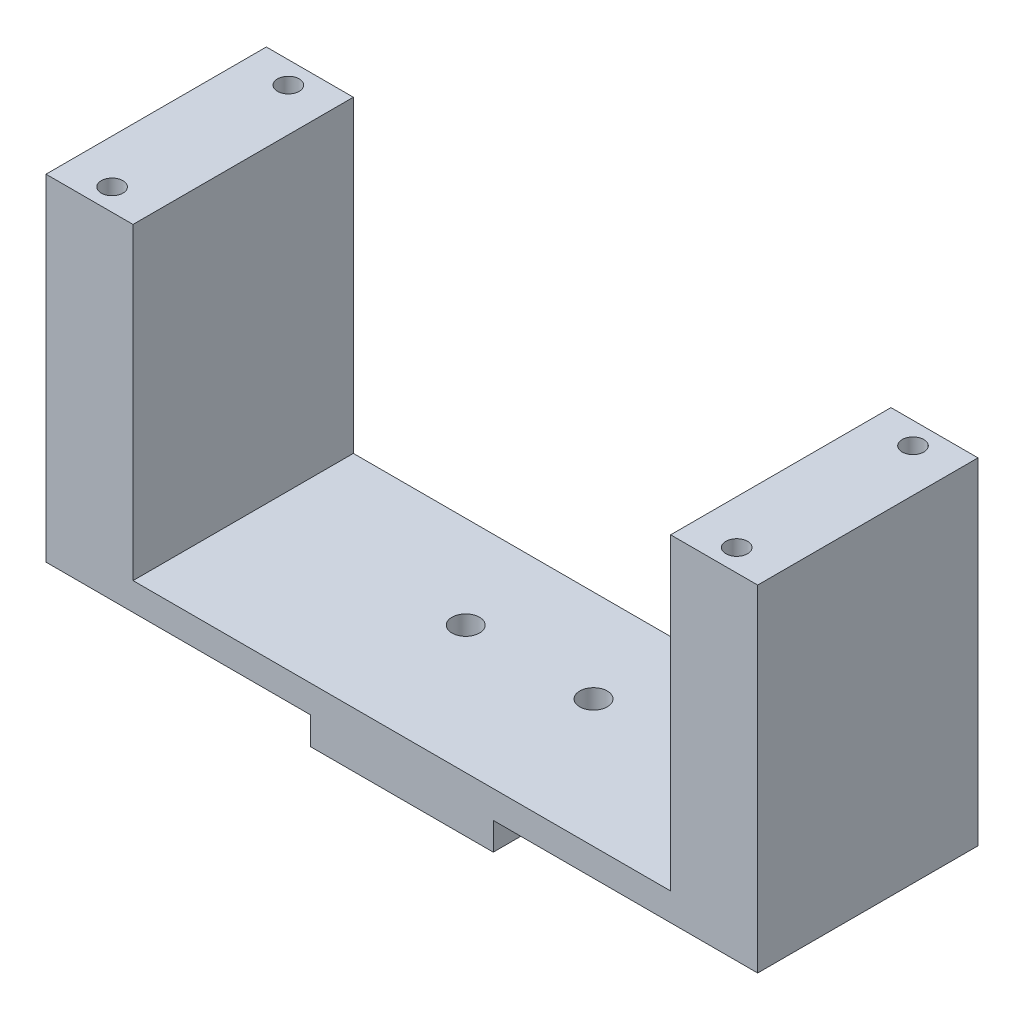
SolidWorks part; units mm, degrees
ref_plane "Front Plane" through (0, 0, 0) normal (0, 0, 1) x (1, 0, 0)
ref_plane "Top Plane" through (0, 0, 0) normal (0, 1, 0) x (1, 0, 0)
ref_plane "Right Plane" through (0, 0, 0) normal (1, 0, 0) x (0, 0, -1)
sketch "Sketch1" plane through (0, 0, 0) normal (0, 1, 0) x (1, 0, 0)
  line L1 (-31.1117, -8.3915) -> (38.7383, -8.3915)
  line L2 (-31.1117, -8.3915) -> (-31.1117, 17.0085)
  line L3 (-31.1117, 17.0085) -> (38.7383, 17.0085)
  line L4 (38.7383, -8.3915) -> (38.7383, 17.0085)
  dimension "D1" = 69.85
  dimension "D2" = 25.4
extrude "Boss-Extrude1" add sketch "Sketch1" along normal blind 3.175
sketch "Sketch2" plane through (0, 3.175, 0) normal (0, 1, 0) x (1, 0, 0)
  line L0 (-31.1117, -8.3915) -> (38.7383, -8.3915) construction
  line L1 (-31.1117, 17.0085) -> (-27.1747, 17.0085)
  line L2 (-31.1117, 17.0085) -> (-31.1117, -8.3915)
  line L3 (-31.1117, -8.3915) -> (-27.1747, -8.3915)
  line L4 (-27.1747, 17.0085) -> (-27.1747, -8.3915)
  line L5 (38.7383, 17.0085) -> (-31.1117, 17.0085) construction
  line L6 (38.7383, 17.0085) -> (34.8013, 17.0085)
  line L7 (38.7383, 17.0085) -> (38.7383, -8.3915)
  line L8 (38.7383, -8.3915) -> (34.8013, -8.3915)
  line L9 (34.8013, 17.0085) -> (34.8013, -8.3915)
  line L10 (38.7383, -8.3915) -> (38.7383, 17.0085) construction
  dimension "D1" = 3.937
  dimension "D2" = 3.937
  dimension "D3" = 0
extrude "Boss-Extrude2" add sketch "Sketch2" along normal blind 35.56 contours L4 L9 L2 L3
sketch "Sketch6" plane through (0, 0, 0) normal (0, -1, 0) x (1, 0, 0)
  line L0 (-31.1117, -17.0085) -> (-31.1117, 8.3915) construction
  line L1 (38.7383, 8.3915) -> (38.7383, -17.0085) construction
  line L2 (38.7383, -17.0085) -> (-31.1117, -17.0085) construction
  circle A0 centre (-3.5527, -6.3405) radius 1.5875
  circle A1 centre (11.1793, -6.3405) radius 1.5875
  dimension "D1" = 3.175
  dimension "D2" = 3.175
  dimension "D3" = 14.732
  dimension "D4" = 27.559
  dimension "D5" = 27.559
  dimension "D6" = 10.668
extrude "Cut-Extrude1" cut sketch "Sketch6" against normal blind 35.56
sketch "Sketch10" plane through (-31.1117, 0, 0) normal (-1, 0, 0) x (0, 0, 1)
  line L1 (-17.0085, 38.735) -> (8.3915, 38.735)
  line L2 (-17.0085, 38.735) -> (-17.0085, 0)
  line L3 (-17.0085, 0) -> (8.3915, 0)
  line L4 (8.3915, 38.735) -> (8.3915, 0)
extrude "Boss-Extrude3" add sketch "Sketch10" along normal blind 6.096
sketch "Sketch11" plane through (38.7383, 0, 0) normal (1, 0, 0) x (0, 0, -1)
  line L1 (17.0085, 38.735) -> (-8.3915, 38.735)
  line L2 (17.0085, 38.735) -> (17.0085, 0)
  line L3 (17.0085, 0) -> (-8.3915, 0)
  line L4 (-8.3915, 38.735) -> (-8.3915, 0)
extrude "Boss-Extrude4" add sketch "Sketch11" along normal blind 6.096
sketch "Sketch14" plane through (0, 38.735, 0) normal (0, 1, 0) x (1, 0, 0)
  line L0 (-37.2077, 17.0085) -> (-27.1747, 17.0085) construction
  line L1 (-37.2077, -8.3915) -> (-27.1747, -8.3915) construction
  line L2 (34.8013, -8.3915) -> (44.8343, -8.3915) construction
  line L3 (44.8343, 17.0085) -> (34.8013, 17.0085) construction
  line L4 (34.8013, 17.0085) -> (34.8013, -8.3915) construction
  line L5 (34.8013, 17.0085) -> (34.8013, -8.3915) construction
  line L6 (-37.2077, -8.3915) -> (-37.2077, 17.0085) construction
  circle A0 centre (-32.1277, 14.4685) radius 1.25
  circle A1 centre (-32.1277, -5.8515) radius 1.25
  circle A2 centre (39.8813, 14.4685) radius 1.25
  circle A3 centre (39.8813, -5.8515) radius 1.25
  point P8 (-32.1912, 17.0085)
  point P13 (39.8178, -8.3915)
  dimension "D6" = 2.5
  dimension "D8" = 2.5
  dimension "D10" = 2.5
  dimension "D12" = 2.5
  dimension "D1" = 2.54
  dimension "D2" = 2.54
  dimension "D3" = 2.54
  dimension "D4" = 2.54
  dimension "D5" = 5.08
  dimension "D7" = 5.08
  dimension "D9" = 5.08
  dimension "D11" = 5.08
extrude "Cut-Extrude2" cut sketch "Sketch14" against normal blind 20.574
sketch "Sketch15" plane through (0, 0, 0) normal (0, -1, 0) x (1, 0, 0)
  line L0 (-37.2077, 8.3915) -> (44.8343, 8.3915) construction
  line L1 (-6.7277, 8.3915) -> (14.3543, 8.3915)
  line L2 (-6.7277, 8.3915) -> (-6.7277, -17.0085)
  line L3 (-6.7277, -17.0085) -> (14.3543, -17.0085)
  line L4 (14.3543, 8.3915) -> (14.3543, -17.0085)
  line L5 (44.8343, -17.0085) -> (-37.2077, -17.0085) construction
  line L6 (-37.2077, -17.0085) -> (-37.2077, 8.3915) construction
  line L7 (44.8343, 8.3915) -> (44.8343, -17.0085) construction
  circle A0 centre (-3.5527, -6.3405) radius 1.5875
  circle A1 centre (11.1793, -6.3405) radius 1.5875
  circle M1 centre (11.1793, -6.3405) radius 1.5875
  circle M2 centre (-3.5527, -6.3405) radius 1.5875
  line M3 (44.8343, 8.3915) -> (-37.2077, 8.3915)
  line M5 (-37.2077, -17.0085) -> (44.8343, -17.0085)
  dimension "D3" = 3.175
  dimension "D4" = 3.175
  dimension "D1" = 30.48
  dimension "D2" = 30.48
extrude "Boss-Extrude6" add sketch "Sketch15" along normal blind 3.175 contours L4 L2 M3 M5 M1 M2
